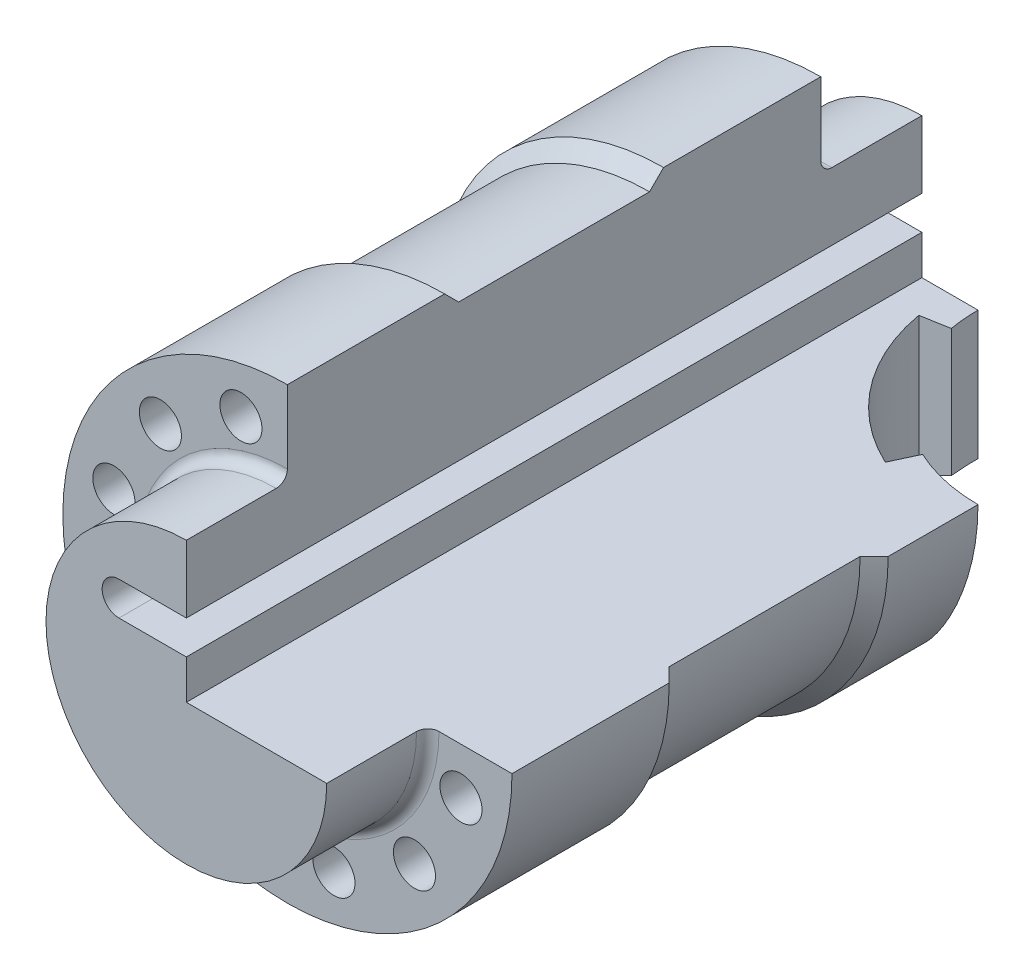
SolidWorks part; units mm, degrees
material "AISI 1020"
ref_plane "Front Plane" through (0, 0, 0) normal (0, 0, 1) x (1, 0, 0)
ref_plane "Top Plane" through (0, 0, 0) normal (0, 1, 0) x (1, 0, 0)
ref_plane "Right Plane" through (0, 0, 0) normal (1, 0, 0) x (0, 0, -1)
sketch "Sketch1" plane through (0, 0, 0) normal (1, 0, 0) x (0, 0, -1)
  line L0 (0, 33.8319) -> (0, -14.886) construction
  line L1 (65.5, 0) -> (-65.5, 0)
  line L2 (-65.5, 0) -> (-65.5, 25)
  line L3 (-65.5, 25) -> (-49.5, 25)
  line L4 (-47.5, 40) -> (-47.5, 27)
  line L5 (-47.5, 40) -> (-19.5, 40)
  line L6 (-19.5, 40) -> (-17, 37.5)
  line L7 (-17, 37.5) -> (17, 37.5)
  line L8 (65.5, 0) -> (65.5, 25)
  line L9 (65.5, 25) -> (49.5, 25)
  line L10 (47.5, 40) -> (47.5, 27)
  line L11 (47.5, 40) -> (19.5, 40)
  line L12 (19.5, 40) -> (17, 37.5)
  arc A0 (-49.5, 25) -> (-47.5, 27) centre (-49.5, 27) ccw
  arc A1 (49.5, 25) -> (47.5, 27) centre (49.5, 27) cw
  point P12 (0, 0)
  point P17 (0, 37.5)
  point P19 (-47.5, 25)
  point P22 (47.5, 25)
  dimension "D3" = 2
  dimension "D4" = 2
  dimension "D1" = 25
  dimension "D2" = 40
  dimension "D5" = 18
  dimension "D6" = 28
  dimension "D7" = 2.5
  dimension "D8" = 45
  dimension "D9" = 131
revolve "Revolve1" add sketch "Sketch1" angle 360 about L1
sketch "Sketch2" plane through (0, 0, 0) normal (0, 0, 1) x (1, 0, 0)
  line L0 (0, 40) -> (0, 13)
  line L1 (0, 0) -> (40, 0)
  line L2 (-12, 10) -> (3.2622, 10) construction
  line L3 (-12, 13) -> (0, 13)
  line L4 (-12, 7) -> (0, 7)
  line L5 (0, 7) -> (0, 0)
  circle A1 centre (0, 0) radius 40 construction
  arc A2 (-12, 13) -> (-12, 7) centre (-12, 10) ccw
  arc A4 (0, 40) -> (40, 0) centre (0, 0) cw
  point P8 (-4.3689, 10)
  dimension "D2" = 3
  dimension "D1" = 7
  dimension "D3" = 12
extrude "Cut-Extrude1" cut sketch "Sketch2" against normal through all both and the other way through all
sketch "Sketch3" plane through (0, 0, 0) normal (0, 1, 0) x (1, 0, 0)
  line L0 (27.3215, 38.3108) -> (25.2084, 33.7792)
  line L1 (10.4558, 60.2906) -> (5.5317, 59.4223)
  line L2 (25, 49.5) -> (25, 65.5) construction
  line L3 (25, 65.5) -> (-25, 65.5) construction
  line L4 (25, 65.5) -> (44.4611, 65.5) construction
  line L5 (40, 47.5) -> (40, 77.2344) construction
  arc A0 (5.5317, 59.4223) -> (25.2084, 33.7792) centre (40, 65.5) ccw
  arc A1 (27.3215, 38.3108) -> (10.4558, 60.2906) centre (40, 65.5) ccw
  point P17 (40, 65.5)
  point P18 (0, 0)
  point P19 (0, 0)
  point P20 (38.3608, 66.7473)
  dimension "D1" = 35
  dimension "D2" = 30
  dimension "D3" = 25
  dimension "D4" = 10
extrude "Cut-Extrude3" cut sketch "Sketch3" against normal through all
sketch "Sketch4" plane through (0, 0, 0) normal (0, 0, 1) x (1, 0, 0)
  line L0 (-8.2822, 30.9096) -> (0, 0) construction
  line L1 (0, 0) -> (0, 32) construction
  circle A0 centre (0, 0) radius 32 construction
  circle A1 centre (-8.2822, 30.9096) radius 3.75
  circle A2 centre (8.2822, 30.9096) radius 3.75
  circle A3 centre (22.6274, 22.6274) radius 3.75
  circle A4 centre (30.9096, 8.2822) radius 3.75
  circle A5 centre (30.9096, -8.2822) radius 3.75
  circle A6 centre (22.6274, -22.6274) radius 3.75
  circle A7 centre (8.2822, -30.9096) radius 3.75
  circle A8 centre (-8.2822, -30.9096) radius 3.75
  circle A9 centre (-22.6274, -22.6274) radius 3.75
  circle A10 centre (-30.9096, -8.2822) radius 3.75
  circle A11 centre (-30.9096, 8.2822) radius 3.75
  circle A12 centre (-22.6274, 22.6274) radius 3.75
  point P31 (0, 0)
  dimension "D1" = 7.5
  dimension "D3" = 64
  dimension "D2" = 15
  dimension "D4" = 12
extrude "Cut-Extrude4" cut sketch "Sketch4" against normal through all both and the other way through all
equation "\"A\"= 131"
equation "\"B\"= 18"
equation "\"C\"= 28"
equation "\"D5@Sketch1\"=\"B\""
equation "\"D6@Sketch1\"=\"C\""
equation "\"D9@Sketch1\"=\"A\""
